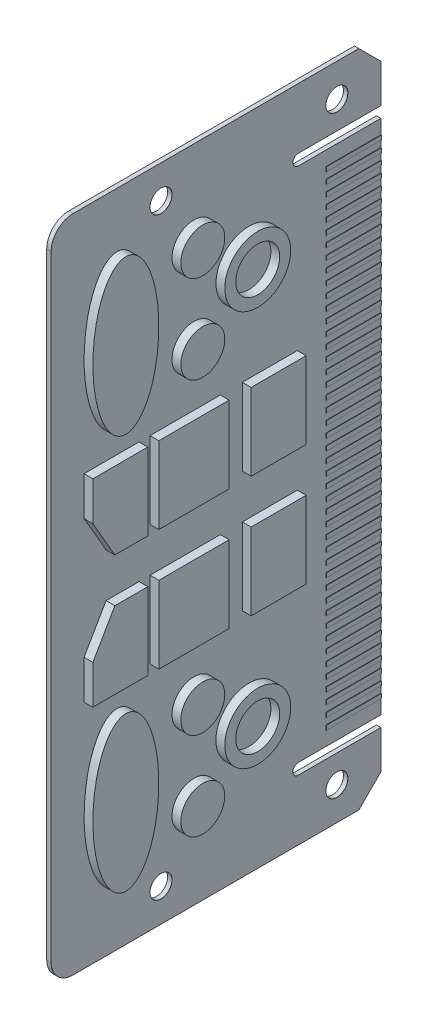
SolidWorks part; units mm, degrees
ref_plane "Front Plane" through (0, 0, 0) normal (1, 0, 0) x (0, 1, 0)
ref_plane "Top Plane" through (0, 0, 0) normal (0, 0, 1) x (0, 1, 0)
ref_plane "Right Plane" through (0, 0, 0) normal (0, 1, 0) x (-1, 0, 0)
sketch "Sketch2" plane through (0, 0, 0) normal (1, 0, 0) x (0, 1, 0)
  line L0 (-300, 150) -> (0, 150)
  line L1 (0, 150) -> (0, 0)
  line L2 (0, 0) -> (-300, 0)
  line L3 (-300, 0) -> (-300, 150)
  dimension "D1" = 300
  dimension "D2" = 150
extrude "base" add sketch "Sketch2" along normal mid plane 2
sketch "Sketch3" plane through (1, 0, 0) normal (1, 0, 0) x (0, 1, 0)
  line L0 (-300, 150) -> (-300, 0) construction
  line L1 (-300, 0) -> (0, 0) construction
  line L2 (0, 0) -> (0, 150) construction
  line L3 (-195, 63) -> (-160, 63)
  line L4 (-195, 63) -> (-195, 38)
  line L5 (-195, 38) -> (-160, 38)
  line L6 (-160, 63) -> (-160, 38)
  line L7 (-195, 105) -> (-160, 105)
  line L8 (-195, 105) -> (-195, 73)
  line L9 (-195, 73) -> (-160, 73)
  line L10 (-160, 105) -> (-160, 73)
  line L11 (-195, 135) -> (-177.3205, 135)
  line L12 (-195, 135) -> (-195, 110)
  line L13 (-195, 110) -> (-160, 110)
  line L14 (-160, 125) -> (-160, 110)
  line L15 (-177.3205, 135) -> (-160, 125)
  line L16 (-150, 150) -> (-150, 0) construction
  line L17 (0, 150) -> (-300, 150) construction
  line L18 (-122.6795, 135) -> (-140, 125)
  line L19 (-140, 125) -> (-140, 110)
  line L20 (-105, 110) -> (-140, 110)
  line L21 (-105, 135) -> (-105, 110)
  line L22 (-105, 135) -> (-122.6795, 135)
  line L23 (-140, 105) -> (-140, 73)
  line L24 (-105, 73) -> (-140, 73)
  line L25 (-105, 105) -> (-105, 73)
  line L26 (-105, 105) -> (-140, 105)
  line L27 (-140, 63) -> (-140, 38)
  line L28 (-105, 38) -> (-140, 38)
  line L29 (-105, 63) -> (-105, 38)
  line L30 (-105, 63) -> (-140, 63)
  circle A0 centre (-260, 85) radius 10
  circle A1 centre (-220, 85) radius 10
  circle A2 centre (-240, 60) radius 15
  circle A3 centre (-240, 60) radius 10
  circle A4 centre (-60, 60) radius 10
  circle A5 centre (-60, 60) radius 15
  circle A6 centre (-80, 85) radius 10
  circle A7 centre (-40, 85) radius 10
  ellipse E0 centre (-240, 120) end of major axis (-205, 120) minor radius 15
  ellipse E1 centre (-60, 120) end of major axis (-95, 120) minor radius 15
  dimension "D1" = 20
  dimension "D2" = 30
  dimension "D8" = 5
  dimension "D3" = 40
  dimension "D4" = 85
  dimension "D5" = 40
  dimension "D6" = 60
  dimension "D7" = 60
  dimension "D9" = 60
  dimension "D10" = 120
  dimension "D11" = 70
  dimension "D12" = 30
  dimension "D13" = 38
  dimension "D14" = 73
  dimension "D15" = 110
  dimension "D16" = 135
  dimension "D17" = 25
  dimension "D18" = 32
  dimension "D19" = 160
  dimension "D20" = 195
  dimension "D21" = 125
  dimension "D22" = 120
extrude "chips" add sketch "Sketch3" along normal blind 4
mirror "mirror_chips" about plane through (0, 0, 0) normal (1, 0, 0) of "chips"
sketch "Sketch4" plane through (1, 0, 0) normal (1, 0, 0) x (0, 1, 0)
  line L0 (-272.5, 37.5) -> (-272.5, 0)
  line L1 (-300, 0) -> (0, 0) construction
  line L2 (-272.5, 0) -> (-267.5, 0)
  line L3 (-267.5, 0) -> (-267.5, 37.5)
  line L4 (-300, 150) -> (-300, 0) construction
  line L5 (-150, 150) -> (-150, 0) construction
  line L6 (0, 150) -> (-300, 150) construction
  line L7 (-32.5, 0) -> (-32.5, 37.5)
  line L8 (-27.5, 0) -> (-32.5, 0)
  line L9 (-27.5, 37.5) -> (-27.5, 0)
  arc A0 (-272.5, 37.5) -> (-267.5, 37.5) centre (-270, 37.5) cw
  arc A1 (-27.5, 37.5) -> (-32.5, 37.5) centre (-30, 37.5) ccw
  dimension "D1" = 5
  dimension "D2" = 27.5
  dimension "D3" = 40
extrude "slot_cut" cut sketch "Sketch4" against normal blind 4
hole_wizard "Ø10.0mm Dowel Hole2" positions "3DSketch2" profile "Sketch10" hole size "Ø10.0" standard "ANSI Metric" end condition through all
sketch3d "3DSketch2"
  line L0 (1, -300, 0) -> (1, -272.5, 0) construction
  line L1 (1, -300, 150) -> (1, -300, 0) construction
  line L2 (1, 0, 0) -> (1, 0, 150) construction
  line L3 (1, -27.5, 0) -> (1, 0, 0) construction
  point P0 (1, -285, 100)
  point P2 (1, -285, 20)
  point P4 (1, -15, 20)
  point P6 (1, -15, 100)
  point P9 (0, 0, 0)
  point P14 (0, 0, 0)
  dimension "D1" = 20
  dimension "D2" = 100
  dimension "D3" = 15
  dimension "D4" = 15
  dimension "D5" = 15
  dimension "D6" = 15
  dimension "D7" = 100
  dimension "D8" = 20
sketch "Sketch10" plane through (1, -285, 100) normal (0, 1, 0) x (0, 0, -1)
  line L0 (0, 0) -> (0, 6)
  line L1 (0, 6) -> (5, 6)
  line L2 (5, 6) -> (5, 0.025)
  line L3 (5, 0.025) -> (5.025, 0)
  line L5 (5.025, 0) -> (0, 0)
  line L6 (-5, 0.025) -> (-5.025, 0) construction
  line L11 (0, -6.35) -> (0, 107.95) construction
  dimension "Thru Hole Dia." = 10
  dimension "Thru Hole Depth" = 6
  dimension "Near C'Sink Dia." = 10.05
  dimension "Near C'Sink Angle" = 90
sketch "Sketch11" plane through (1, 0, 0) normal (1, 0, 0) x (0, 1, 0)
  line L0 (-267.5, 0) -> (-32.5, 0) construction
  line L1 (-261, 0) -> (-259, 0)
  line L2 (-261, 0) -> (-261, 25)
  line L3 (-261, 25) -> (-259, 25)
  line L4 (-259, 0) -> (-259, 25)
  line L5 (-267.5, 0) -> (-267.5, 37.5) construction
  point P8 (-260, 25)
  point P9 (-260, 0)
  dimension "D1" = 2
  dimension "D2" = 6.5
  dimension "D3" = 25
extrude "contact" add sketch "Sketch11" along normal blind 0.2
pattern_linear "contact_pattern" count 45 spacing 5 along (0, 1, 0) of "contact"
fillet "Fillet1" radius 10 2 edges at (0, 0, 150) (0, -300, 150)
chamfer "Chamfer1" distance 10 angle 45 2 edges at (0, 0, 0) (0, -300, 0)
